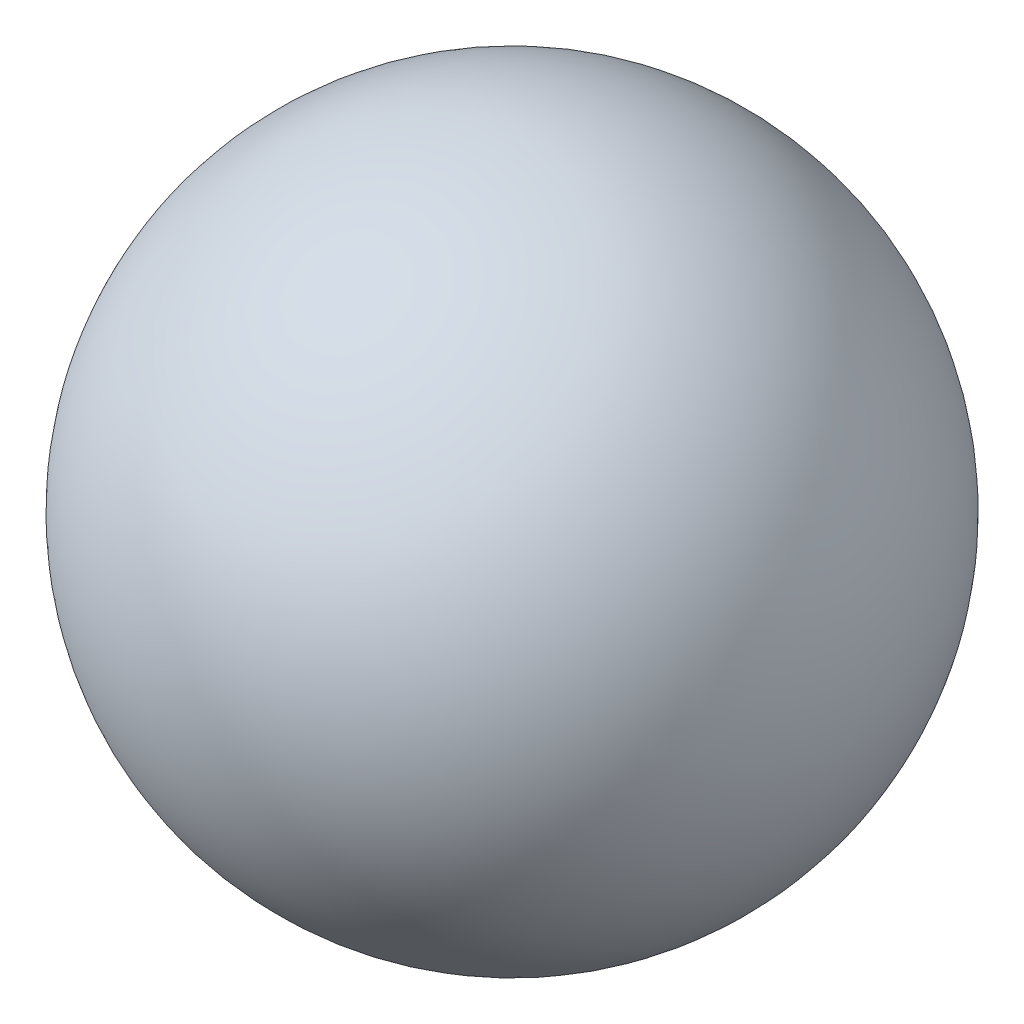
SolidWorks part; units mm, degrees
material "Chrome Stainless Steel"
ref_plane "Front Plane" through (0, 0, 0) normal (0, 0, 1) x (1, 0, 0)
ref_plane "Top Plane" through (0, 0, 0) normal (0, 1, 0) x (1, 0, 0)
ref_plane "Right Plane" through (0, 0, 0) normal (1, 0, 0) x (0, 0, -1)
sketch "RevolveS" plane through (0, 0, 0) normal (0, 0, 1) x (1, 0, 0)
  line L0 (0.5, 0) -> (-0.5, 0) construction
  line L1 (0.5, 0) -> (-0.5, 0)
  arc A0 (0.5, 0) -> (-0.5, 0) centre (0, 0) ccw
  dimension "Dia" = 1
revolve "Revolve" add sketch "RevolveS" angle 360 about L0
